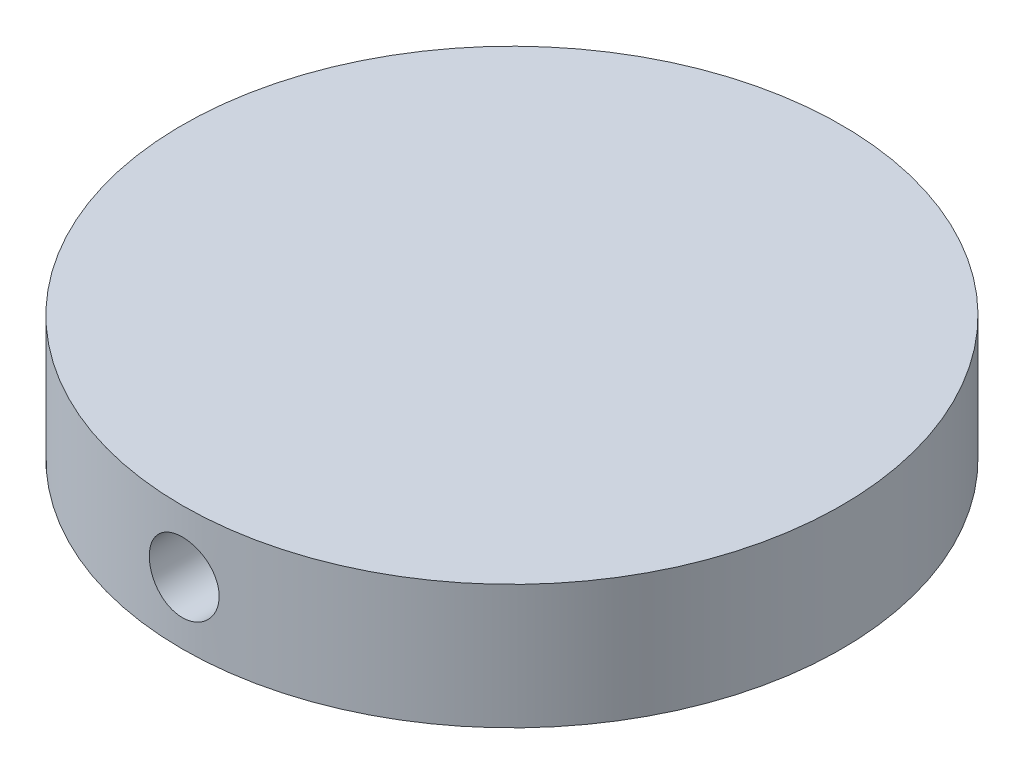
SolidWorks part; units mm, degrees
ref_plane "Front Plane" through (0, 0, 0) normal (0, 0, 1) x (1, 0, 0)
ref_plane "Top Plane" through (0, 0, 0) normal (0, 1, 0) x (1, 0, 0)
ref_plane "Right Plane" through (0, 0, 0) normal (1, 0, 0) x (0, 0, -1)
sketch "Sketch2" plane through (0, 0, 0) normal (0, 1, 0) x (1, 0, 0)
  circle A0 centre (0, 0) radius 26.9427
extrude "Boss-Extrude1" add sketch "Sketch2" along normal blind 10.16
sketch "Sketch3" plane through (0, 0, 0) normal (0, 0, 1) x (1, 0, 0)
  line L0 (0, 0) -> (0, 10.16) construction
  line L1 (26.9427, 10.16) -> (-26.9427, 10.16) construction
  line L2 (-26.9427, 5.08) -> (26.9427, 5.08) construction
  line L3 (-26.9427, 10.16) -> (-26.9427, 0) construction
  line L4 (26.9427, 0) -> (26.9427, 10.16) construction
  circle A0 centre (0, 5.08) radius 2.8548
extrude "Cut-Extrude1" cut sketch "Sketch3" against normal through all and the other way through all
